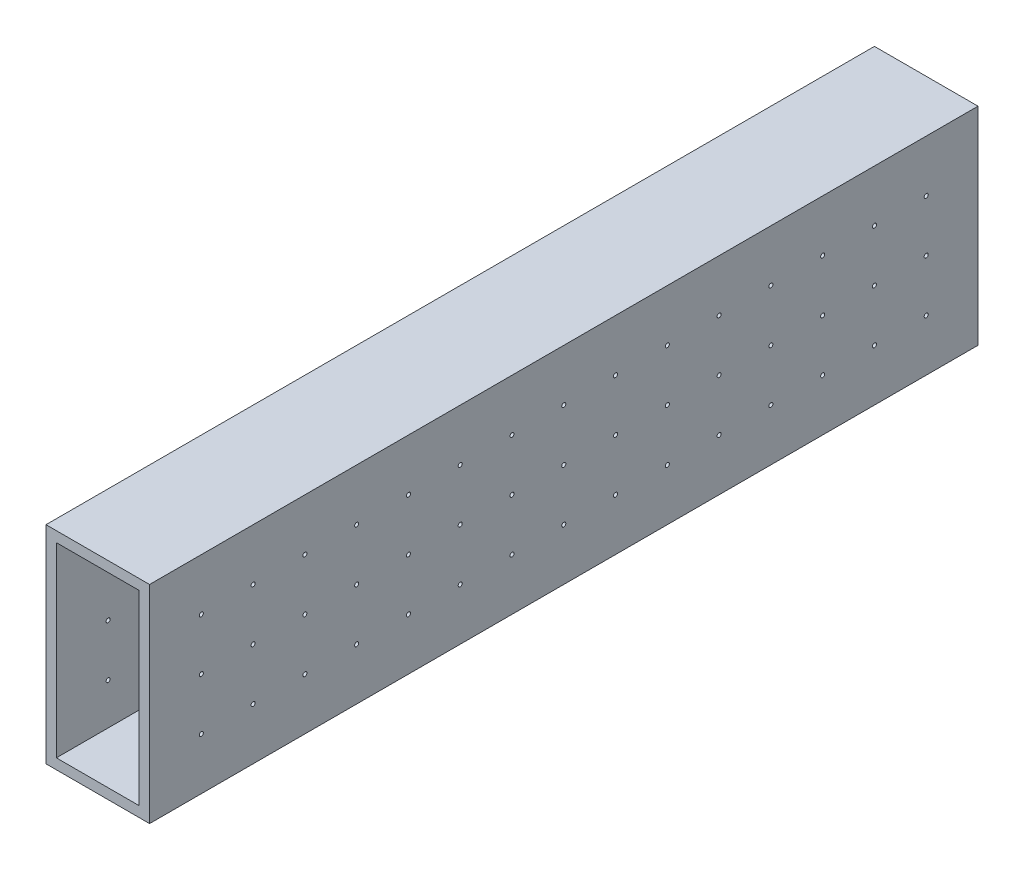
SolidWorks part; units mm, degrees
ref_plane "Front Plane" through (0, 0, 0) normal (0, 0, 1) x (1, 0, 0)
ref_plane "Top Plane" through (0, 0, 0) normal (0, 1, 0) x (1, 0, 0)
ref_plane "Right Plane" through (0, 0, 0) normal (1, 0, 0) x (0, 0, -1)
sketch "Sketch1" plane through (0, 0, 0) normal (0, 0, 1) x (1, 0, 0)
  line L1 (6.5054, 14.179) -> (26.8254, 14.179)
  line L2 (6.5054, 14.179) -> (6.5054, -31.541)
  line L3 (6.5054, -31.541) -> (26.8254, -31.541)
  line L4 (26.8254, 14.179) -> (26.8254, -31.541)
  line L5 (3.9654, 16.719) -> (29.3654, 16.719)
  line L6 (3.9654, 16.719) -> (3.9654, -34.081)
  line L7 (3.9654, -34.081) -> (29.3654, -34.081)
  line L8 (29.3654, 16.719) -> (29.3654, -34.081)
  dimension "D1" = 50.8
  dimension "D2" = 25.4
  dimension "D3" = 2.54
  dimension "D4" = 2.54
  dimension "D5" = 2.54
  dimension "D6" = 2.54
extrude "Boss-Extrude1" add sketch "Sketch1" along normal blind 203.2
sketch "Sketch2" plane through (29.3654, 0, 0) normal (1, 0, 0) x (0, 0, -1)
  line L0 (-203.2, 16.719) -> (0, 16.719) construction
  line L1 (-203.2, -34.081) -> (-203.2, 16.719) construction
  circle A0 centre (-190.5, 4.019) radius 0.5
  circle A1 centre (-177.8, 4.019) radius 0.5
  circle A2 centre (-165.1, 4.019) radius 0.5
  circle A3 centre (-152.4, 4.019) radius 0.5
  circle A4 centre (-139.7, 4.019) radius 0.5
  circle A5 centre (-127, 4.019) radius 0.5
  circle A6 centre (-114.3, 4.019) radius 0.5
  circle A7 centre (-101.6, 4.019) radius 0.5
  circle A8 centre (-88.9, 4.019) radius 0.5
  circle A9 centre (-76.2, 4.019) radius 0.5
  circle A10 centre (-63.5, 4.019) radius 0.5
  circle A11 centre (-50.8, 4.019) radius 0.5
  circle A12 centre (-38.1, 4.019) radius 0.5
  circle A13 centre (-25.4, 4.019) radius 0.5
  circle A14 centre (-12.7, 4.019) radius 0.5
  circle A15 centre (-177.8, -8.681) radius 0.5
  circle A16 centre (-165.1, -8.681) radius 0.5
  circle A17 centre (-152.4, -8.681) radius 0.5
  circle A18 centre (-139.7, -8.681) radius 0.5
  circle A19 centre (-127, -8.681) radius 0.5
  circle A20 centre (-114.3, -8.681) radius 0.5
  circle A21 centre (-101.6, -8.681) radius 0.5
  circle A22 centre (-88.9, -8.681) radius 0.5
  circle A23 centre (-76.2, -8.681) radius 0.5
  circle A24 centre (-63.5, -8.681) radius 0.5
  circle A25 centre (-50.8, -8.681) radius 0.5
  circle A26 centre (-38.1, -8.681) radius 0.5
  circle A27 centre (-25.4, -8.681) radius 0.5
  circle A28 centre (-12.7, -8.681) radius 0.5
  circle A29 centre (-177.8, -21.381) radius 0.5
  circle A30 centre (-165.1, -21.381) radius 0.5
  circle A31 centre (-152.4, -21.381) radius 0.5
  circle A32 centre (-139.7, -21.381) radius 0.5
  circle A33 centre (-127, -21.381) radius 0.5
  circle A34 centre (-114.3, -21.381) radius 0.5
  circle A35 centre (-101.6, -21.381) radius 0.5
  circle A36 centre (-88.9, -21.381) radius 0.5
  circle A37 centre (-76.2, -21.381) radius 0.5
  circle A38 centre (-63.5, -21.381) radius 0.5
  circle A39 centre (-50.8, -21.381) radius 0.5
  circle A40 centre (-38.1, -21.381) radius 0.5
  circle A41 centre (-25.4, -21.381) radius 0.5
  circle A42 centre (-12.7, -21.381) radius 0.5
  circle A43 centre (-190.5, -8.681) radius 0.5
  circle A44 centre (-190.5, -21.381) radius 0.5
  dimension "D1" = 1
  dimension "D2" = 12.7
  dimension "D3" = 12.7
  dimension "D4" = 15
  dimension "D5" = 3
extrude "Cut-Extrude1" cut sketch "Sketch2" against normal through all
